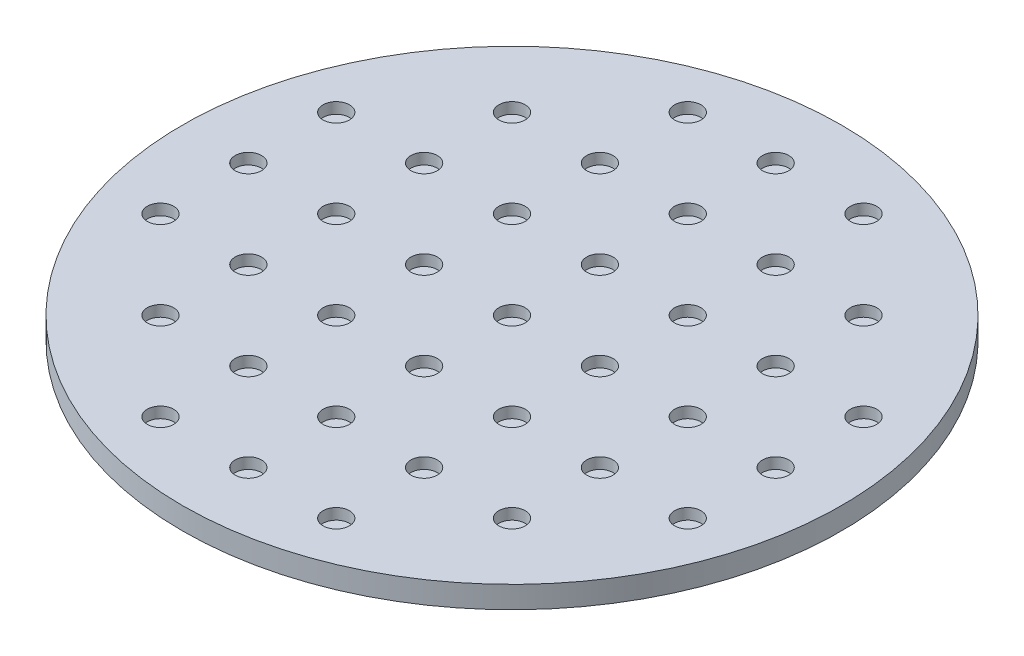
SolidWorks part; units mm, degrees
material "PE High Density"
ref_plane "Front Plane" through (0, 0, 0) normal (0, 0, 1) x (1, 0, 0)
ref_plane "Top Plane" through (0, 0, 0) normal (0, 1, 0) x (1, 0, 0)
ref_plane "Right Plane" through (0, 0, 0) normal (1, 0, 0) x (0, 0, -1)
sketch "Sketch1" plane through (0, 0, 0) normal (0, 1, 0) x (1, 0, 0)
  circle A0 centre (0, 0) radius 381
  dimension "D1" = 762
extrude "Boss-Extrude1" add sketch "Sketch1" along normal mid plane 25.4
sketch "Sketch6" plane through (0, 12.7, 0) normal (0, 1, 0) x (1, 0, 0)
  line L0 (101.6, 101.6) -> (101.6, 203.2) construction
  line L1 (101.6, -101.6) -> (101.6, -203.2) construction
  line L2 (101.6, -101.6) -> (203.2, -101.6) construction
  line L3 (-101.6, 101.6) -> (-203.2, 101.6) construction
  circle A0 centre (0, 0) radius 15.25
  circle A1 centre (-101.6, 0) radius 15.25
  circle A2 centre (101.6, 0) radius 15.25
  circle A3 centre (-101.6, 101.6) radius 15.25
  circle A4 centre (0, 101.6) radius 15.25
  circle A5 centre (101.6, 101.6) radius 15.25
  circle A6 centre (-101.6, -101.6) radius 15.25
  circle A7 centre (0, -101.6) radius 15.25
  circle A8 centre (101.6, -101.6) radius 15.25
  circle A9 centre (101.6, 203.2) radius 15.25
  circle A10 centre (0, 203.2) radius 15.25
  circle A11 centre (-101.6, 203.2) radius 15.25
  circle A12 centre (101.6, 304.8) radius 15.25
  circle A13 centre (0, 304.8) radius 15.25
  circle A14 centre (-101.6, 304.8) radius 15.25
  circle A15 centre (101.6, -203.2) radius 15.25
  circle A16 centre (0, -203.2) radius 15.25
  circle A17 centre (-101.6, -203.2) radius 15.25
  circle A18 centre (101.6, -304.8) radius 15.25
  circle A19 centre (0, -304.8) radius 15.25
  circle A20 centre (-101.6, -304.8) radius 15.25
  circle A21 centre (203.2, -101.6) radius 15.25
  circle A22 centre (203.2, 0) radius 15.25
  circle A23 centre (203.2, 101.6) radius 15.25
  circle A24 centre (304.8, -101.6) radius 15.25
  circle A25 centre (304.8, 0) radius 15.25
  circle A26 centre (304.8, 101.6) radius 15.25
  circle A27 centre (-203.2, 101.6) radius 15.25
  circle A28 centre (-203.2, 0) radius 15.25
  circle A29 centre (-203.2, -101.6) radius 15.25
  circle A30 centre (-304.8, 101.6) radius 15.25
  circle A31 centre (-304.8, 0) radius 15.25
  circle A32 centre (-304.8, -101.6) radius 15.25
  circle A33 centre (-203.2, 203.2) radius 15.25
  circle A34 centre (203.2, 203.2) radius 15.25
  circle A35 centre (203.2, -203.2) radius 15.25
  circle A36 centre (-203.2, -203.2) radius 15.25
  dimension "D1" = 101.6
  dimension "D2" = 101.6
  dimension "D3" = 30.5
  dimension "D4" = 101.6
  dimension "D5" = 101.6
  dimension "D12" = 30.5
  dimension "D14" = 101.6
  dimension "D15" = 101.6
  dimension "D16" = 101.6
  dimension "D7" = 101.6
  dimension "D9" = 101.6
  dimension "D10" = 101.6
  dimension "D11" = 101.6
  dimension "D6" = 3
  dimension "D8" = 3
  dimension "D13" = 3
extrude "Cut-Extrude1" cut sketch "Sketch6" against normal blind 12.7
